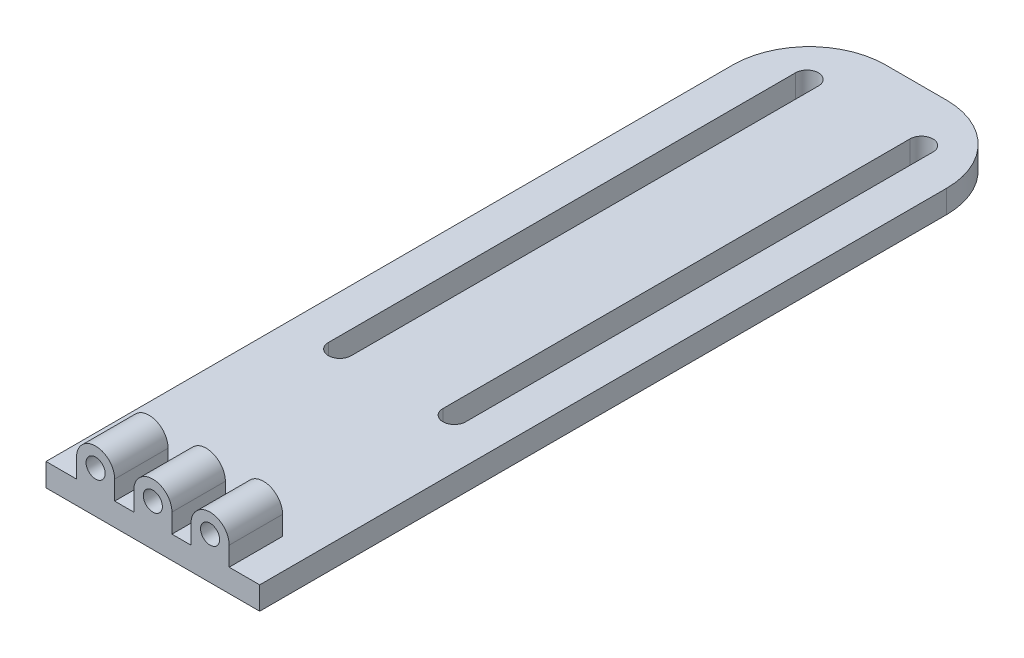
SolidWorks part; units mm, degrees
ref_plane "Alzado" through (0, 0, 0) normal (0, 0, 1) x (1, 0, 0)
ref_plane "Planta" through (0, 0, 0) normal (0, 1, 0) x (1, 0, 0)
ref_plane "Vista lateral" through (0, 0, 0) normal (1, 0, 0) x (0, 0, -1)
sketch "Croquis1" plane through (0, 0, 0) normal (0, 1, 0) x (1, 0, 0)
  line L0 (-14, 0) -> (14, 0) construction
  line L2 (-14, 0) -> (14, 0)
  line L3 (-14, 0) -> (-14, 100)
  line L4 (-14, 100) -> (14, 100)
  line L5 (14, 0) -> (14, 100)
  point P4 (0, 0)
extrude "Saliente-Extruir1" add sketch "Croquis1" along normal blind 3
sketch "Croquis2" plane through (0, 3, 0) normal (0, 1, 0) x (1, 0, 0)
  line L5 (14, 0) -> (14, 100) construction
  line L6 (-14, 0) -> (14, 0)
  line L7 (-14, 0) -> (-14, 7)
  line L8 (-14, 7) -> (14, 7)
  line L9 (14, 0) -> (14, 7)
extrude "Saliente-Extruir2" add sketch "Croquis2" along normal blind 5
sketch "Croquis3" plane through (0, 0, 0) normal (0, 0, 1) x (1, 0, 0)
  line L2 (0, 5.5) -> (7.5, 5.5) construction
  line L3 (7.5, 5.5) -> (0, 5.5) construction
  line L4 (0, 5.5) -> (-7.5, 5.5) construction
  circle A0 centre (-7.5, 5.5) radius 1.25
  circle A1 centre (0, 5.5) radius 1.25
  circle A2 centre (7.5, 5.5) radius 1.25
extrude "Cortar-Extruir2" cut sketch "Croquis3" against normal up to next
sketch "Croquis4" plane through (0, 0, 0) normal (0, 0, 1) x (1, 0, 0)
  line L0 (-10, 3) -> (-14, 3)
  line L1 (-14, 3) -> (-14, 8)
  line L3 (-10, 5.5) -> (-10, 3)
  line L7 (14, 8) -> (14, 3)
  line L8 (14, 8) -> (14, 0) construction
  line L9 (14, 3) -> (10, 3)
  line L10 (10, 3) -> (10, 5.5)
  line L11 (5, 5.5) -> (5, 3)
  line L12 (5, 3) -> (2.5, 3)
  line L13 (2.5, 3) -> (2.5, 5.5)
  line L14 (-2.5, 5.5) -> (-2.5, 3)
  line L16 (-5, 3) -> (-5, 5.5)
  line L17 (-5, 3) -> (-2.5, 3)
  line L18 (-14, 8) -> (-14, 10.2005)
  line L19 (-14, 10.2005) -> (14, 10.2005)
  line L20 (14, 10.2005) -> (14, 8)
  arc A0 (-5, 5.5) -> (-10, 5.5) centre (-7.5, 5.5) ccw
  arc A1 (2.5, 5.5) -> (-2.5, 5.5) centre (0, 5.5) ccw
  arc A2 (10, 5.5) -> (5, 5.5) centre (7.5, 5.5) ccw
extrude "Cortar-Extruir3" cut sketch "Croquis4" against normal up to next
sketch "Croquis5" plane through (0, 3, 0) normal (0, 1, 0) x (1, 0, 0)
  line L0 (0, 0) -> (0, 50000) construction
  line L1 (14, 100) -> (-14, 100) construction
  line L2 (0, 0) -> (0, 32) construction
  line L3 (14, 32) -> (-14, 32) construction
  line L4 (-14, 100) -> (-14, 0) construction
  line L5 (7.5, 32) -> (-7.5, 32) construction
  line L6 (-7.5, 32) -> (-7.5, 17) construction
  line L7 (-7.5, 17) -> (-7.5, 93.2085) construction
  line L8 (-7.5, 93.2085) -> (7.5, 93.2085) construction
  line L9 (-7.5, 32) -> (-7.5, 93.2085) construction
  line L10 (-9, 32) -> (-9, 93.2085)
  line L11 (-6, 32) -> (-6, 93.2085)
  line L12 (7.5, 32) -> (7.5, 93.2085) construction
  line L13 (9, 32) -> (9, 93.2085)
  line L14 (6, 32) -> (6, 93.2085)
  arc A0 (-9, 32) -> (-6, 32) centre (-7.5, 32) ccw
  arc A1 (-6, 93.2085) -> (-9, 93.2085) centre (-7.5, 93.2085) ccw
  arc A2 (9, 32) -> (6, 32) centre (7.5, 32) cw
  arc A3 (6, 93.2085) -> (9, 93.2085) centre (7.5, 93.2085) cw
  point P5 (0, 100)
  point P13 (0, 32)
  point P15 (0, 32)
  point P16 (0, 32)
  point P20 (-7.5, 62.6042)
  point P25 (7.5, 62.6042)
extrude "Cortar-Extruir4" cut sketch "Croquis5" against normal blind 10
fillet "Redondeo1" radius 10 2 edges at (-14, 1.5, -100) (14, 1.5, -100)
